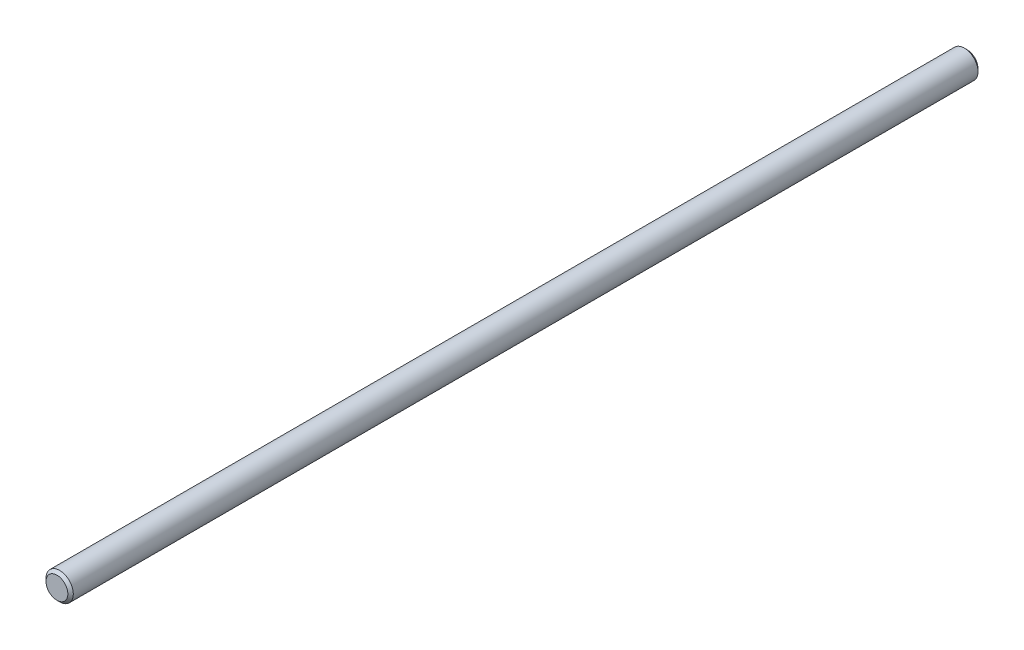
SolidWorks part; units mm, degrees
ref_plane "Front" through (0, 0, 0) normal (0, 0, 1) x (1, 0, 0)
ref_plane "Top" through (0, 0, 0) normal (0, 1, 0) x (1, 0, 0)
ref_plane "Right" through (0, 0, 0) normal (1, 0, 0) x (0, 0, -1)
sketch "Sketch1" plane through (0, 0, 0) normal (0, 0, 1) x (1, 0, 0)
  circle A0 centre (0, 0) radius 6
  dimension "D1" = 12
extrude "Extrude1" add sketch "Sketch1" along normal mid plane 400
chamfer "Chamfer1" distance 1.2 angle 45 2 edges at (6, 0, -200) (6, 0, 200)
equation "\"D1@Chamfer1\" = \"D1@Sketch1\" * .1"
